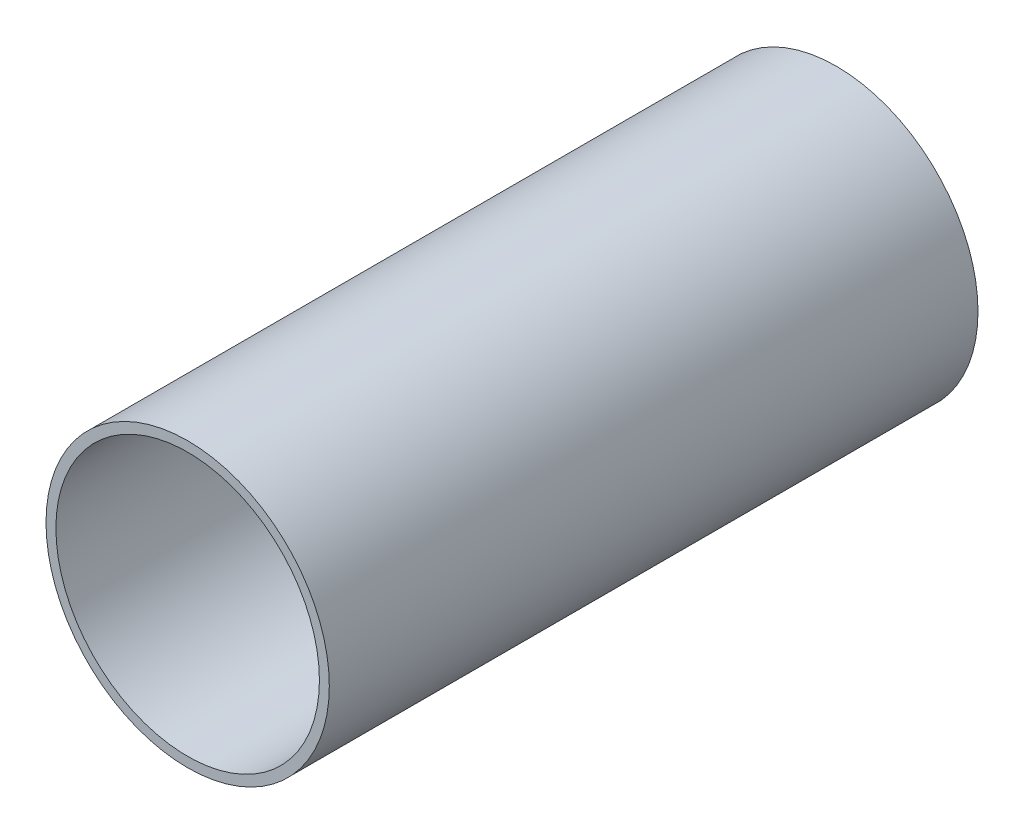
SolidWorks part; units mm, degrees
material "Balsa"
ref_plane "Front Plane" through (0, 0, 0) normal (0, 0, 1) x (1, 0, 0)
ref_plane "Top Plane" through (0, 0, 0) normal (0, 1, 0) x (1, 0, 0)
ref_plane "Right Plane" through (0, 0, 0) normal (1, 0, 0) x (0, 0, -1)
sketch "Sketch1" plane through (0, 0, 0) normal (0, 0, 1) x (1, 0, 0)
  circle A0 centre (0, 0) radius 20.6375
  circle A1 centre (0, 0) radius 22.1869
extrude "Boss-Extrude1" add sketch "Sketch1" along normal blind 101.6
